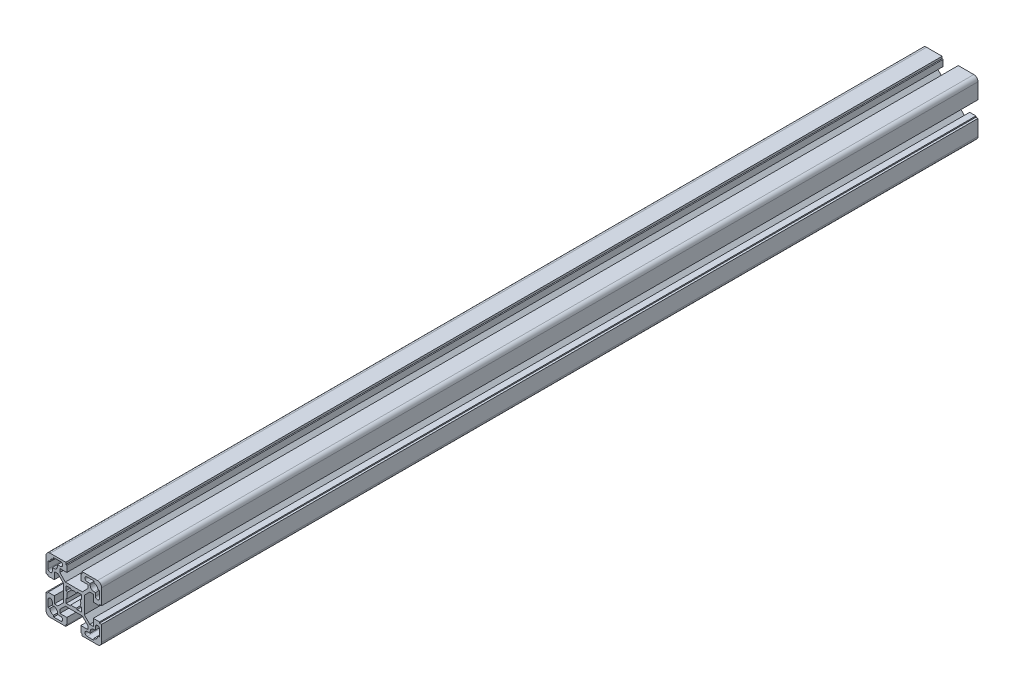
SolidWorks part; units mm, degrees
material "6061 Alloy"
ref_plane "Front Plane" through (0, 0, 0) normal (0, 0, 1) x (1, 0, 0)
ref_plane "Top Plane" through (0, 0, 0) normal (0, 1, 0) x (1, 0, 0)
ref_plane "Right Plane" through (0, 0, 0) normal (1, 0, 0) x (0, 0, -1)
sketch "Sketch1" plane through (0, 0, 0) normal (0, 0, 1) x (1, 0, 0)
  line L0 (5.8, -20) -> (17, -20)
  line L1 (14, -10.05) -> (11.4642, -10.05)
  line L2 (0, -21.1722) -> (0, 18.817) construction
  line L3 (0, 21.1722) -> (0, -18.817) construction
  line L4 (14.5, -18.5) -> (9.5, -18.5)
  line L5 (18.5, 5) -> (14, 5)
  line L6 (6.0858, -7.5) -> (10.05, -11.4642)
  line L7 (20, 5.8) -> (18.5, 5.8)
  line L8 (14, 5) -> (14, 10.05)
  line L9 (18.5, 5.8) -> (18.5, 5)
  line L10 (18.5, 14.5) -> (17.25, 14.5)
  line L11 (14.5, 11.75) -> (15.5, 11.75)
  line L12 (14.5, 17.25) -> (14.5, 18.5)
  line L13 (18.5, 9.5) -> (18.5, 14.5)
  line L14 (15.5, 11.75) -> (15.5, 9.5)
  line L15 (20, 17) -> (20, 5.8)
  line L16 (5.5, 5.5) -> (2.3979, 5.5)
  line L17 (2.3979, 5.5) -> (1.9983, 4.5833)
  line L18 (5.5, 2.3979) -> (5.5, 5.5)
  line L19 (4.5833, 1.9983) -> (5.5, 2.3979)
  line L20 (5, -14) -> (5, -18.5)
  line L21 (11.4642, 10.05) -> (7.5, 6.0858)
  line L22 (-6.0858, 7.5) -> (6.0858, 7.5)
  line L23 (11.75, 15.5) -> (11.75, 14.5)
  line L24 (5, -18.5) -> (5.8, -18.5)
  line L25 (5.8, -18.5) -> (5.8, -20)
  line L26 (10.05, -11.4642) -> (10.05, -14)
  line L27 (10.05, -14) -> (5, -14)
  line L28 (9.5, -15.5) -> (11.75, -15.5)
  line L29 (11.75, -15.5) -> (11.75, -14.5)
  line L30 (9.5, 15.5) -> (11.75, 15.5)
  line L31 (10.05, 14) -> (5, 14)
  line L32 (10.05, 11.4642) -> (10.05, 14)
  line L33 (5.8, 18.5) -> (5.8, 20)
  line L34 (5, 18.5) -> (5.8, 18.5)
  line L35 (7.5, -6.0858) -> (7.5, 6.0858)
  line L36 (5, 14) -> (5, 18.5)
  line L37 (6.0858, 7.5) -> (10.05, 11.4642)
  line L38 (14.5, 18.5) -> (9.5, 18.5)
  line L39 (14, 10.05) -> (11.4642, 10.05)
  line L40 (5.8, 20) -> (17, 20)
  line L41 (-18.5, -5) -> (-14, -5)
  line L42 (-6.0858, -7.5) -> (6.0858, -7.5)
  line L43 (11.4642, -10.05) -> (7.5, -6.0858)
  line L44 (-20, -5.8) -> (-18.5, -5.8)
  line L45 (-14, -5) -> (-14, -10.05)
  line L46 (-18.5, -5.8) -> (-18.5, -5)
  line L47 (-18.5, -14.5) -> (-17.25, -14.5)
  line L48 (4.5833, -1.9983) -> (5.5, -2.3979)
  line L49 (5.5, -2.3979) -> (5.5, -5.5)
  line L50 (2.3979, -5.5) -> (1.9983, -4.5833)
  line L51 (5.5, -5.5) -> (2.3979, -5.5)
  line L52 (-14.5, -11.75) -> (-15.5, -11.75)
  line L53 (-14.5, -17.25) -> (-14.5, -18.5)
  line L54 (-18.5, -9.5) -> (-18.5, -14.5)
  line L55 (-15.5, -11.75) -> (-15.5, -9.5)
  line L56 (-20, -17) -> (-20, -5.8)
  line L57 (-5.5, -5.5) -> (-2.3979, -5.5)
  line L58 (-2.3979, -5.5) -> (-1.9983, -4.5833)
  line L59 (-5.5, -2.3979) -> (-5.5, -5.5)
  line L60 (-4.5833, -1.9983) -> (-5.5, -2.3979)
  line L61 (-11.4642, -10.05) -> (-7.5, -6.0858)
  line L62 (-5.8, 20) -> (-17, 20)
  line L63 (-14, 10.05) -> (-11.4642, 10.05)
  line L64 (-14.5, 18.5) -> (-9.5, 18.5)
  line L65 (-6.0858, 7.5) -> (-10.05, 11.4642)
  line L66 (-5, 14) -> (-5, 18.5)
  line L67 (-7.5, -6.0858) -> (-7.5, 6.0858)
  line L68 (-5, 18.5) -> (-5.8, 18.5)
  line L69 (-5.8, 18.5) -> (-5.8, 20)
  line L70 (-10.05, 11.4642) -> (-10.05, 14)
  line L71 (-10.05, 14) -> (-5, 14)
  line L72 (-9.5, 15.5) -> (-11.75, 15.5)
  line L73 (-11.75, -15.5) -> (-11.75, -14.5)
  line L74 (-9.5, -15.5) -> (-11.75, -15.5)
  line L75 (-10.05, -14) -> (-5, -14)
  line L76 (-10.05, -11.4642) -> (-10.05, -14)
  line L77 (-5.8, -18.5) -> (-5.8, -20)
  line L78 (-5, -18.5) -> (-5.8, -18.5)
  line L79 (-11.75, 15.5) -> (-11.75, 14.5)
  line L80 (-11.4642, 10.05) -> (-7.5, 6.0858)
  line L81 (-5, -14) -> (-5, -18.5)
  line L82 (-4.5833, 1.9983) -> (-5.5, 2.3979)
  line L83 (-5.5, 2.3979) -> (-5.5, 5.5)
  line L84 (-2.3979, 5.5) -> (-1.9983, 4.5833)
  line L85 (-5.5, 5.5) -> (-2.3979, 5.5)
  line L86 (-20, 17) -> (-20, 5.8)
  line L87 (-15.5, 11.75) -> (-15.5, 9.5)
  line L88 (20, -17) -> (20, -5.8)
  line L89 (15.5, -11.75) -> (15.5, -9.5)
  line L90 (18.5, -9.5) -> (18.5, -14.5)
  line L91 (14.5, -17.25) -> (14.5, -18.5)
  line L92 (14.5, -11.75) -> (15.5, -11.75)
  line L93 (18.5, -14.5) -> (17.25, -14.5)
  line L94 (-18.5, 9.5) -> (-18.5, 14.5)
  line L95 (-14.5, 17.25) -> (-14.5, 18.5)
  line L96 (18.5, -5.8) -> (18.5, -5)
  line L97 (14, -5) -> (14, -10.05)
  line L98 (20, -5.8) -> (18.5, -5.8)
  line L99 (18.5, -5) -> (14, -5)
  line L100 (-14.5, 11.75) -> (-15.5, 11.75)
  line L101 (-18.5, 14.5) -> (-17.25, 14.5)
  line L102 (-18.5, 5.8) -> (-18.5, 5)
  line L103 (-14, 5) -> (-14, 10.05)
  line L104 (-20, 5.8) -> (-18.5, 5.8)
  line L105 (-6.0858, -7.5) -> (-10.05, -11.4642)
  line L106 (-18.5, 5) -> (-14, 5)
  line L107 (-14.5, -18.5) -> (-9.5, -18.5)
  line L108 (-20, 0) -> (20.788, 0) construction
  line L109 (-14, -10.05) -> (-11.4642, -10.05)
  line L110 (-5.8, -20) -> (-17, -20)
  arc A0 (14.5, -11.75) -> (11.75, -14.5) centre (14.5, -14.5) ccw
  arc A1 (18.5, 9.5) -> (15.5, 9.5) centre (17, 9.5) cw
  arc A2 (14.5, 17.25) -> (17.25, 14.5) centre (14.5, 14.5) cw
  arc A3 (17, 20) -> (20, 17) centre (17, 17) cw
  arc A4 (-1.9983, 4.5833) -> (1.9983, 4.5833) centre (0, 0) cw
  arc A5 (9.5, 15.5) -> (9.5, 18.5) centre (9.5, 17) cw
  arc A6 (9.5, -15.5) -> (9.5, -18.5) centre (9.5, -17) ccw
  arc A7 (14.5, 11.75) -> (11.75, 14.5) centre (14.5, 14.5) cw
  arc A8 (4.5833, -1.9983) -> (4.5833, 1.9983) centre (0, 0) ccw
  arc A9 (-18.5, -9.5) -> (-15.5, -9.5) centre (-17, -9.5) cw
  arc A10 (-14.5, -17.25) -> (-17.25, -14.5) centre (-14.5, -14.5) cw
  arc A11 (-1.9983, -4.5833) -> (1.9983, -4.5833) centre (0, 0) ccw
  arc A12 (-17, -20) -> (-20, -17) centre (-17, -17) cw
  arc A13 (-4.5833, -1.9983) -> (-4.5833, 1.9983) centre (0, 0) cw
  arc A14 (-14.5, 11.75) -> (-11.75, 14.5) centre (-14.5, 14.5) ccw
  arc A15 (-9.5, -15.5) -> (-9.5, -18.5) centre (-9.5, -17) cw
  arc A16 (-9.5, 15.5) -> (-9.5, 18.5) centre (-9.5, 17) ccw
  arc A17 (-17, 20) -> (-20, 17) centre (-17, 17) ccw
  arc A18 (17, -20) -> (20, -17) centre (17, -17) ccw
  arc A19 (14.5, -17.25) -> (17.25, -14.5) centre (14.5, -14.5) ccw
  arc A20 (18.5, -9.5) -> (15.5, -9.5) centre (17, -9.5) ccw
  arc A21 (-14.5, 17.25) -> (-17.25, 14.5) centre (-14.5, 14.5) ccw
  arc A22 (-18.5, 9.5) -> (-15.5, 9.5) centre (-17, 9.5) ccw
  arc A23 (-14.5, -11.75) -> (-11.75, -14.5) centre (-14.5, -14.5) cw
  point P55 (7.5, 0)
  point P101 (-7.5, 0)
  point P116 (0, -7.5)
  point P149 (0, 7.5)
extrude "Extrude1" add sketch "Sketch1" along normal mid plane 630
hole_wizard "M12 Tapped Hole1" positions "3DSketch2" profile "Sketch3" tap size "M12" standard "ISO"
sketch3d "3DSketch2"
  line L0 (-20, 17, 0) -> (-20, 5.8, 0) construction
  line L1 (-5.8, 20, 0) -> (-17, 20, 0) construction
  line L2 (-5.8, 20, 200) -> (-17, 20, 200) construction
  line L3 (-20, 17, 200) -> (-20, 5.8, 200) construction
  point P0 (0, 0, 200)
  point P2 (0, 0, 0)
  dimension "D1" = 20
  dimension "D2" = 20
  dimension "D3" = 20
  dimension "D4" = 20
sketch "Sketch3" plane through (0, 0, 200) normal (1, 0, 0) x (0, -1, 0)
  line L0 (0, 0) -> (0, 35.8144)
  line L1 (0, 35.8144) -> (5.1, 32.75)
  line L2 (5.1, 32.75) -> (5.1, 0.925)
  line L3 (5.1, 0.925) -> (6.025, 0)
  line L5 (6.025, 0) -> (0, 0)
  line L6 (-5.1, 0.925) -> (-6.025, 0) construction
  line L10 (0, 35.8144) -> (-5.1, 32.75) construction
  line L11 (0, -6.35) -> (0, 107.95) construction
  dimension "Tap Drill Dia." = 10.2
  dimension "Tap Drill Depth" = 32.75
  dimension "Near C'Sink Dia." = 12.05
  dimension "Near C'Sink Angle" = 90
  dimension "Drill Angle" = 118
cosmetic thread "Hole Thread1" [suppressed] parameters "D1"=24, "D2"=12
cosmetic thread "Hole Thread2" [suppressed] parameters "D1"=24, "D2"=12
hole_wizard "Ø9.8 (9.8) Diameter Hole1" positions "3DSketch3" profile "Sketch4" hole size "Ø9.8" standard "ISO"
sketch3d "3DSketch3"
  line L0 (-5.8, 20, 200) -> (-17, 20, 200) construction
  line L1 (20, -17, 200) -> (20, -5.8, 200) construction
  line L2 (17, 20, 0) -> (5.8, 20, 0) construction
  line L3 (20, -17, 0) -> (20, -5.8, 0) construction
  point P0 (0, 20, 184)
  point P2 (20, 0, 184)
  point P4 (0, 20, 16)
  point P6 (20, 0, 16)
  dimension "D1" = 16
  dimension "D2" = 20
  dimension "D3" = 20
  dimension "D4" = 16
  dimension "D5" = 16
  dimension "D6" = 16
sketch "Sketch4" plane through (0, 20, 184) normal (1, 0, 0) x (0, 0, 1)
  line L0 (0, 0) -> (0, 40)
  line L1 (0, 40) -> (4.9, 40)
  line L2 (4.9, 40) -> (4.9, 0)
  line L5 (4.9, 0) -> (0, 0)
  line L11 (0, -6.35) -> (0, 107.95) construction
  dimension "Thru Hole Dia." = 9.8
  dimension "Thru Hole Depth" = 40
hole_wizard "Ø17.0 (17) Diameter Hole1" positions "3DSketch4" profile "Sketch5" hole size "Ø17.0" standard "ISO"
sketch3d "3DSketch4"
  line L0 (-5.8, 20, 200) -> (-17, 20, 200) construction
  line L1 (-5.8, 20, 0) -> (-17, 20, 0) construction
  point P0 (0, 20, 177.5)
  point P2 (0, 20, 22.5)
  dimension "D1" = 20
  dimension "D2" = 22.5
  dimension "D3" = 22.5
sketch "Sketch5" plane through (0, 20, 177.5) normal (1, 0, 0) x (0, 0, 1)
  line L0 (0, 0) -> (0, 40)
  line L1 (0, 40) -> (8.5, 40)
  line L2 (8.5, 40) -> (8.5, 0)
  line L5 (8.5, 0) -> (0, 0)
  line L11 (0, -6.35) -> (0, 107.95) construction
  dimension "Thru Hole Dia." = 17
  dimension "Thru Hole Depth" = 40
